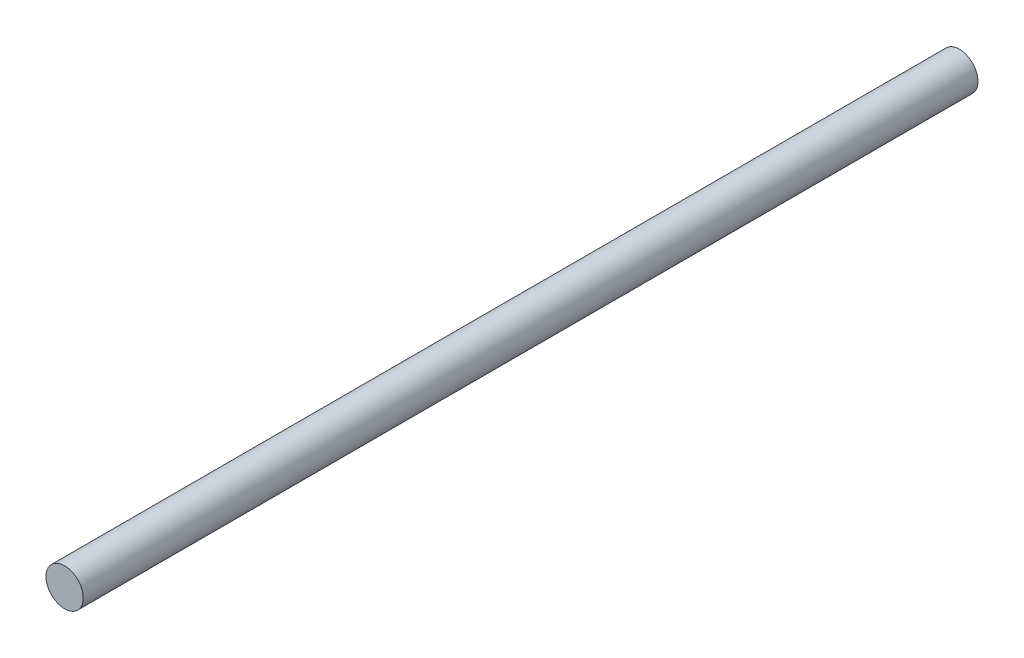
SolidWorks part; units mm, degrees
ref_plane "Front Plane" through (0, 0, 0) normal (0, 0, 1) x (1, 0, 0)
ref_plane "Top Plane" through (0, 0, 0) normal (0, 1, 0) x (1, 0, 0)
ref_plane "Right Plane" through (0, 0, 0) normal (1, 0, 0) x (0, 0, -1)
sketch "Sketch1" plane through (0, 0, 0) normal (0, 0, 1) x (1, 0, 0)
  circle A0 centre (0, 0) radius 1.5875
  dimension "D1" = 3.175
extrude "Boss-Extrude1" add sketch "Sketch1" along normal blind 76.2
